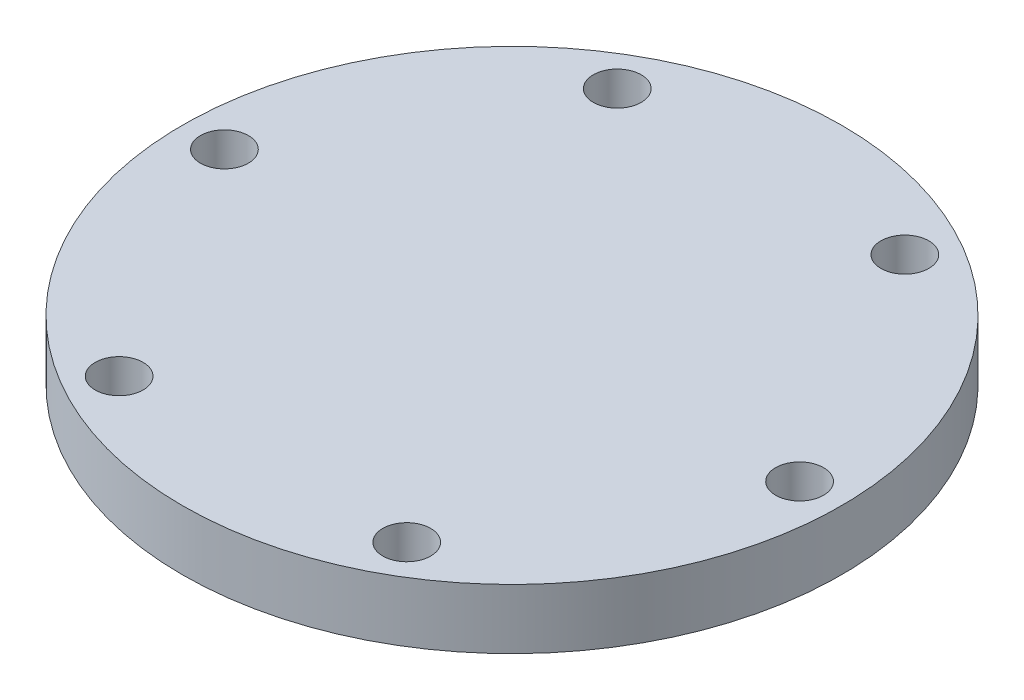
SolidWorks part; units mm, degrees
material "Delrin 2700 NC010, Ацеталь сополимер низкой вязкости (SS)"
ref_plane "Спереди" through (0, 0, 0) normal (0, 0, 1) x (1, 0, 0)
ref_plane "Сверху" through (0, 0, 0) normal (0, 1, 0) x (1, 0, 0)
ref_plane "Справа" through (0, 0, 0) normal (1, 0, 0) x (0, 0, -1)
sketch "Эскиз1" plane through (0, 0, 0) normal (0, 1, 0) x (1, 0, 0)
  line L1 (23.9982, 0) -> (11.9991, 20.783)
  line L2 (11.9991, 20.783) -> (-11.9991, 20.783)
  line L3 (-11.9991, 20.783) -> (-23.9982, 0)
  line L4 (-23.9982, 0) -> (-11.9991, -20.783)
  line L5 (-11.9991, -20.783) -> (11.9991, -20.783)
  line L6 (11.9991, -20.783) -> (23.9982, 0)
  circle A0 centre (0, 0) radius 24
  circle A1 centre (0, 0) radius 20.783 construction
  circle A2 centre (-23.9982, 0) radius 2
  circle A3 centre (-11.9991, 20.783) radius 2
  circle A4 centre (11.9991, 20.783) radius 2
  circle A5 centre (23.9982, 0) radius 2
  circle A6 centre (11.9991, -20.783) radius 2
  circle A7 centre (-11.9991, -20.783) radius 2
  circle A8 centre (0, 0) radius 27.5
  point P23 (0, 0)
  dimension "D1" = 6
  dimension "D2" = 48
extrude "Бобышка-Вытянуть1" add sketch "Эскиз1" along normal blind 5 contours A8 A7 A0 A2 A3 A4 A5 A6 | A3 A0 A2 L3 | A4 A0 A3 L2 | A5 A0 A4 L1 | A7 L5 A6 L6 A5 L1 A4 L2 A3 L3 A2 L4 | A6 A0 A5 L6 | A7 A0 A6 L5 | A7 L4 A2 A0
